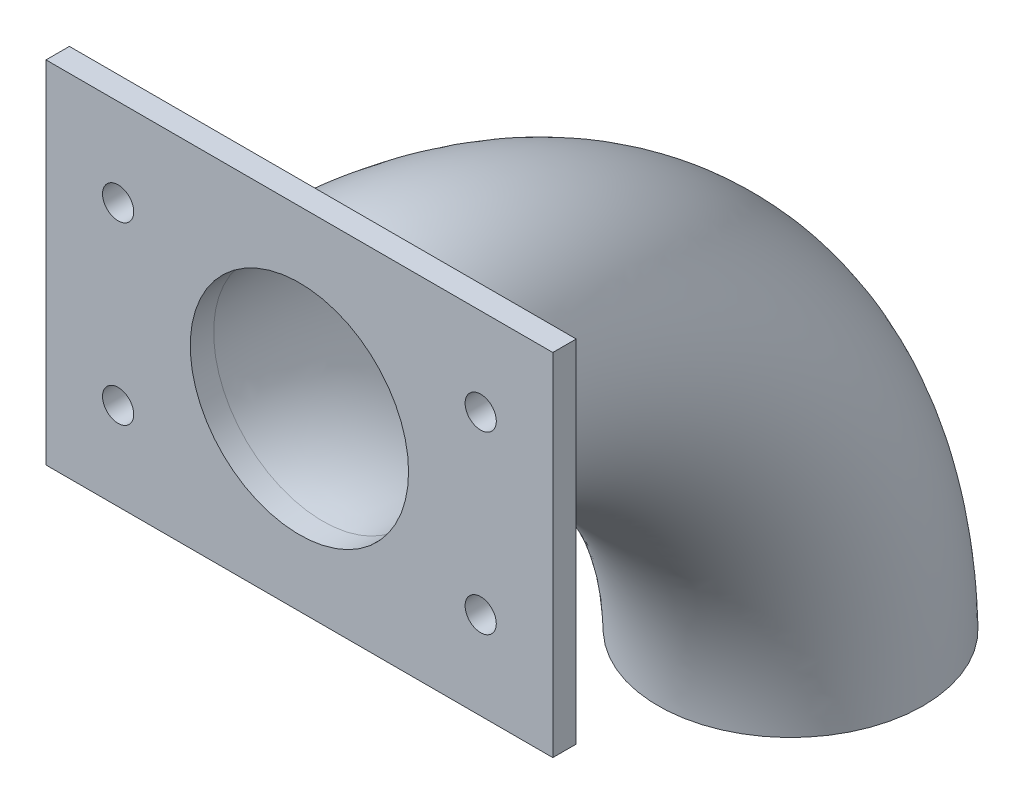
SolidWorks part; units mm, degrees
ref_plane "Plan de face" through (0, 0, 0) normal (0, 0, 1) x (1, 0, 0)
ref_plane "Plan de dessus" through (0, 0, 0) normal (0, 1, 0) x (1, 0, 0)
ref_plane "Plan de droite" through (0, 0, 0) normal (1, 0, 0) x (0, 0, -1)
sketch "Esquisse1" plane through (0, 0, 0) normal (0, 0, 1) x (1, 0, 0)
  circle A0 centre (0, 0) radius 14
  circle A1 centre (0, 0) radius 17
  dimension "D1" = 28
  dimension "D2" = 3
sketch "Esquisse2" plane through (0, 0, 0) normal (1, 0, 0) x (0, 0, -1)
  line L0 (0, 0) -> (0, -56) construction
  line L1 (0, -56) -> (60, -56) construction
  arc A0 (0, 0) -> (60, -56) centre (2, -58) cw
  dimension "D1" = 56
  dimension "D2" = 60
sweep "Balayage1" add profiles "Esquisse1" path "Esquisse2"
sketch "Esquisse3" plane through (0, 0, 0) normal (0, 0, 1) x (1, 0, 0)
  line L0 (-32.5, 0) -> (-14, 0) construction
  line L1 (-32.5, 22.5) -> (32.5, 22.5)
  line L2 (-32.5, 22.5) -> (-32.5, -22.5)
  line L3 (-32.5, -22.5) -> (32.5, -22.5)
  line L4 (32.5, 22.5) -> (32.5, -22.5)
  line L5 (-32.5, 22.5) -> (32.5, -22.5) construction
  line L6 (-32.5, -22.5) -> (32.5, 22.5) construction
  line L7 (0, 22.5) -> (0, -22.5) construction
  line L8 (-23.25, 0) -> (-23.25, 22.5) construction
  circle A0 centre (0, 0) radius 14
  circle A1 centre (-23.25, 11.25) radius 2
  circle A2 centre (-23.25, -11.25) radius 2
  circle A3 centre (23.25, -11.25) radius 2
  circle A4 centre (23.25, 11.25) radius 2
  point P0 (0, 0)
  dimension "D3" = 4
  dimension "D4" = 9.25
  dimension "D1" = 65
  dimension "D2" = 45
extrude "Boss.-Extru.1" add sketch "Esquisse3" along normal blind 3
